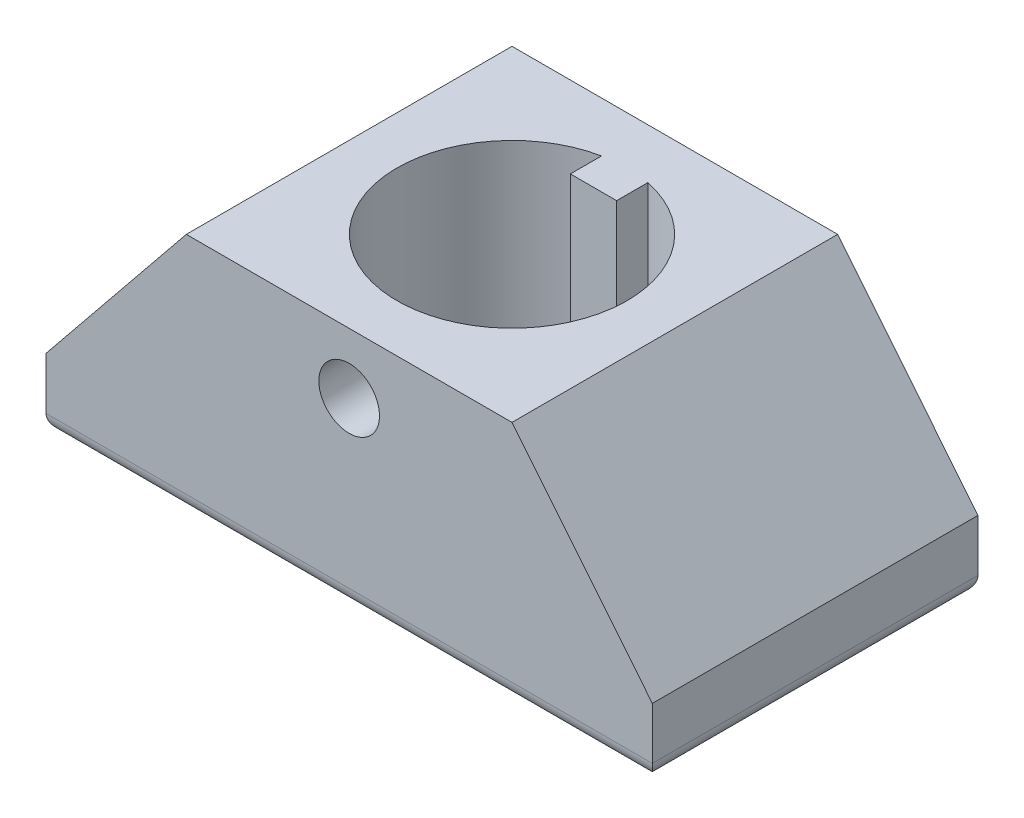
SolidWorks part; units mm, degrees
ref_plane "Front Plane" through (0, 0, 0) normal (0, 0, 1) x (1, 0, 0)
ref_plane "Top Plane" through (0, 0, 0) normal (0, 1, 0) x (1, 0, 0)
ref_plane "Right Plane" through (0, 0, 0) normal (1, 0, 0) x (0, 0, -1)
sketch "Sketch1" plane through (0, 0, 0) normal (0, 1, 0) x (1, 0, 0)
  line L0 (-1.335, 6.5044) -> (-1.335, 4.7044)
  line L1 (-1.335, 4.7044) -> (1.335, 4.7044)
  line L2 (1.335, 4.7044) -> (1.335, 6.5044)
  line L4 (-9.4, -9.4) -> (9.4, -9.4)
  line L5 (-9.4, -9.4) -> (-9.4, 9.4)
  line L6 (-9.4, 9.4) -> (9.4, 9.4)
  line L7 (9.4, -9.4) -> (9.4, 9.4)
  line L8 (-9.4, -9.4) -> (9.4, 9.4) construction
  line L9 (-9.4, 9.4) -> (9.4, -9.4) construction
  arc A1 (-1.335, 6.5044) -> (1.335, 6.5044) centre (0, 0) ccw
  dimension "D1" = 13.28
  dimension "D2" = 18.8
  dimension "D3" = 1.8
  dimension "D4" = 2.67
  dimension "D5" = 1.335
  dimension "D6" = 18.8
extrude "Boss-Extrude1" add sketch "Sketch1" along normal blind 10
sketch "Sketch5" plane through (0, 0, -4.7044) normal (0, 0, 1) x (1, 0, 0)
  line L1 (1.335, 10) -> (-1.335, 10) construction
  circle A0 centre (-0.0001, 6.5) radius 1.75
  dimension "D1" = 3.5
  dimension "D2" = 3.5
extrude "Cut-Extrude3" cut sketch "Sketch5" along normal blind 15
sketch "Sketch6" plane through (0, 0, 0) normal (0, -1, 0) x (1, 0, 0)
  line L1 (17.5, -9.4) -> (-17.5, -9.4)
  line L2 (17.5, -9.4) -> (17.5, 9.4)
  line L3 (17.5, 9.4) -> (-17.5, 9.4)
  line L4 (-17.5, -9.4) -> (-17.5, 9.4)
  line L5 (17.5, -9.4) -> (-17.5, 9.4) construction
  line L6 (17.5, 9.4) -> (-17.5, -9.4) construction
  point P0 (0, 0)
  dimension "D1" = 18.8
  dimension "D2" = 35
extrude "Boss-Extrude2" add sketch "Sketch6" along normal blind 4
sketch "Sketch7" plane through (0, 0, 9.4) normal (0, 0, 1) x (1, 0, 0)
  line L0 (-9.4, 10) -> (-9.4, 0)
  line L1 (-9.4, 0) -> (-17.5, 0)
  line L2 (-17.5, 0) -> (-9.4, 10)
  line L3 (9.4, 0) -> (17.5, 0)
  line L4 (17.5, 0) -> (9.4, 10)
  line L5 (9.4, 10) -> (9.4, 0)
extrude "Boss-Extrude3" add sketch "Sketch7" against normal up to surface (18.8 mm away) up to face at (-1.0125, 2.75, -9.4)
fillet "Fillet4" radius 1 4 edges at (17.5, -4, 0) (0, -4, -9.4) (-17.5, -4, 0) (0, -4, 9.4)
sketch "Sketch8" plane through (0, 0, 0) normal (0, 1, 0) x (1, 0, 0)
  line L0 (1.335, 4.7044) -> (-1.335, 4.7044) construction
  line L1 (1.335, 6.5044) -> (1.335, 4.7044) construction
  line L2 (-1.335, 4.7044) -> (-1.335, 6.5044) construction
  line L3 (1.335, 4.7044) -> (-1.335, 4.7044)
  line L4 (1.335, 6.5044) -> (1.335, 4.7044)
  line L5 (-1.335, 4.7044) -> (-1.335, 6.5044)
  arc A0 (-1.335, 6.5044) -> (1.335, 6.5044) centre (0, 0) ccw construction
  arc A1 (-1.335, 6.5044) -> (1.335, 6.5044) centre (0, 0) ccw
extrude "Cut-Extrude4" cut sketch "Sketch8" against normal blind 4
fillet "Fillet5" radius 0.5 4 edges at (-1.335, -4, -5.6044) (0, -4, -4.7044) (1.335, -4, -5.6044) (0, -4, 6.64)
equation "\"CageLeftBottomEdge\"=22.11mm"
equation "\"CageLeftTopEdge\"=22.11mm"
equation "\"CageRightBottomEdge\"=21.63mm"
equation "\"CageRightTopEdge\"=21.63mm"
equation "\"CageHeight\"=86.04mm"
equation "\"CageLength\"=73.76mm"
equation "\"CageTopScrewClearance\"=10mm"
equation "\"CageBottomScrewClearance\"=25mm"
equation "\"CageLeftTopDepth\"= 11.65mm"
equation "\"CageLeftBottomDepth\"=11.11mm"
equation "\"CageLeftTopHeight\"=8.56175mm"
equation "\"CageLeftBottomHeight\"=16mm"
equation "\"CageRightTopDepth\"= 11.05mm"
equation "\"CageRightBottomDepth\"=10.58mm"
equation "\"CageRightTopHeight\"=9.6mm"
equation "\"CageRightBottomHeight\"=15.49mm"
equation "\"CageLeftTopChannelDepth\"=2.41908mm"
equation "\"CageLeftBottomChannelDepth\"=2.588mm"
equation "\"CageLeftChannelHeight\"=11.7mm"
equation "\"CageRightTopChannelDepth\"=2.32mm"
equation "\"CageRightBottomChannelDepth\"=2.318mm"
equation "\"CageRightChannelHeight\"=10mm"
equation "\"CageChanRelHeight\"=23.99mm"
equation "\"CageChanRelDepth\"=5.492mm"
equation "\"CageChamberRadius\"=16.261mm"
equation "\"CageScrewDiameter\"=4.8mm"
equation "\"CageSetScrewDiameter\"=3.5mm"
equation "\"CageAxleRadius\"=6.639mm"
equation "\"CageAxleKeyHeight\"=1.619mm"
equation "\"CageAxleKeyWidth\"=2.662mm"
equation "\"CageHoseWindowWidth\"=16.29mm"
equation "\"CageHoseWindowHeight\"=26.5mm"
equation "\"CageHoseWindow-Edge\"=8.89mm"
equation "\"CageScrew-VerticalEdge\"=5.0mm"
equation "\"CageScrew-HorizontalEdge\"=7.5mm"
equation "\"CageScrew-HoseCornerScrewEdge\"=4.45mm"
equation "\"CageAxle-BottomEdge\"=56.05mm"
equation "\"CageAxle-FrontEdge\"=46.03mm"
equation "\"CageBackSetScrew-Axle\"=40mm"
equation "\"CageFrontSetScrew-Axle\"=22mm"
equation "\"CageVelocityWindow-BackEdge\"=34.8mm"
equation "\"CageVelocityWindow-BottomEdge\"=27.55mm"
equation "\"CageVelocityWindowHeight\"=22.29mm"
equation "\"CageVelocityWindowWidth\"=12.61mm"
equation "\"TriggerSlot-BottomEdge\"=6.35mm"
equation "\"TriggerSlot-FrontEdge\"=15mm"
equation "\"TriggerSlotSize\"=6.7mm"
equation "\"TriggerRackOffset\"=6mm"
equation "\"TriggerSlotSizeInt\"=.25in"
equation "\"MotorMountLegLength\"=.25in"
equation "\"GearOffset\"=.264907in"
equation "\"TriggerSlotSpacing\"=.25in"
equation "\"TriggerMiniSlotWidth\"=3.5mm"
equation "\"TriggerRackWidth\"=6.5mm"
equation "\"pandiscradius\"=14in"
equation "\"towermaterialwidth\"=.25in"
equation "\"towerslotlength\"=.5in"
equation "\"towermarkerspace\"=5in"
equation "\"towerslothorizoffset\"=1in"
equation "\"towerslothorizspacing\"=2in"
equation "\"towerslotvertoffset\"=3in"
equation "\"towerslotvertspacing\"=1in"
equation "\"towerheight\"=12in"
equation "\"towerupslot\"=1in"
equation "\"toweraxle\"=.5in"
equation "\"stepperouterrad\"=10mm"
equation "\"stepperscrewsize\"=3.45mm"
equation "\"stepperscrewc2c\"=49.5mm"
equation "\"stepperdepthoffset\"=24mm"
equation "\"stepperhorizoffset\"=22.91mm"
equation "\"shaftslotOD\"=18.8mm"
equation "\"shaftslotID\"=13.28mm"
equation "\"shaftkeywidth\"=2.67mm"
equation "\"shaftkeydepth\"=1.8mm"
equation "\"shaftcollartotaldepth\"=12.5mm"
equation "\"shaftsquaredepth\"=6mm"
equation "\"shaftsetscrewsize\"=3.5mm"
equation "\"shaftkeytightdepth\"=1.85mm"
equation "\"shaftslottightID\"=12.78mm"
equation "\"D3@Sketch1\"=\"shaftkeydepth\""
equation "\"D4@Sketch1\"=\"shaftkeywidth\""
equation "\"D5@Sketch1\"=\"shaftkeywidth\"/2"
equation "\"D1@Sketch1\"=\"shaftslotID\""
equation "\"D6@Sketch1\"=\"shaftslotOD\""
equation "\"D2@Sketch1\"=\"shaftslotOD\""
equation "\"D1@Sketch6\"=\"shaftslotOD\""
equation "\"cagecollartotaldepth\"=10mm"
equation "\"D1@Boss-Extrude1\"=\"cagecollartotaldepth\""
equation "\"D1@Sketch5\"=\"shaftsetscrewsize\""
equation "\"D2@Sketch5\"=\"shaftsetscrewsize\""
equation "\"cagecollartotalwidth\"=35mm"
equation "\"D2@Sketch6\"=\"cagecollartotalwidth\""
equation "\"cagecollarbasedepth\"=4mm"
equation "\"D1@Boss-Extrude2\"=\"cagecollarbasedepth\""
equation "\"shaftsetscrewoffset\"=9mm"
equation "\"gearhubintdiam\"=30mm"
equation "\"gearhubintwid\"=15mm"
equation "\"towerspeedwidth\"=2in"
equation "\"towerspeedheight\"=8in"
equation "\"towerspeedgap\"=2in"
equation "\"stepperaxleflat\"=.037in"
equation "\"stepperaxlerad\"=0.11811024in"
equation "\"ajaxaxlesize\"=3.87mm"
equation "\"ajaxinnercut\"=2.3mm"
equation "\"ajaxwidth\"=6.1mm"
equation "\"ajaxdiametral\"=25.8854"
equation "\"ajaxcutoutdepth\"=2.3mm"
equation "\"ajax4020gap\"=29.5mm"
equation "\"ajax4010gap\"=24.5mm"
equation "\"ajax20hubbuffer\"=6.1mm"
equation "\"ajax20hubholeoffset\"=.19685in"
equation "\"ajax20hubholesize\"=.059055in"
equation "\"ajax20cutoutint\"=13.4mm"
equation "\"ajax40hubholesize\"=7.21mm"
equation "\"ajax40hubholeoffset\"=10mm"
equation "\"ajax40hubbuffer\"=8.9mm"
equation "\"ajax40cutoutint\"=32.6mm"
equation "\"bearingpandiscrad\"=6.8in"
equation "\"bearingpandiscang\"=48.75deg"
equation "\"bearingclearholedist\"=4.7345in"
equation "\"bearingclearholesize\"=.5in"
equation "\"bearingclearholeang\"=22.5deg"
equation "\"bearingmountholedist\"=4.25in"
equation "\"bearingwirehole\"=1.5in"
equation "\"no6diam\"=.146in"
equation "\"shortconangle\"=20deg"
equation "\"shortconlen\"=.875in"
equation "\"longconlen\"=1.25in"
equation "\"longconangle\"=15deg"
